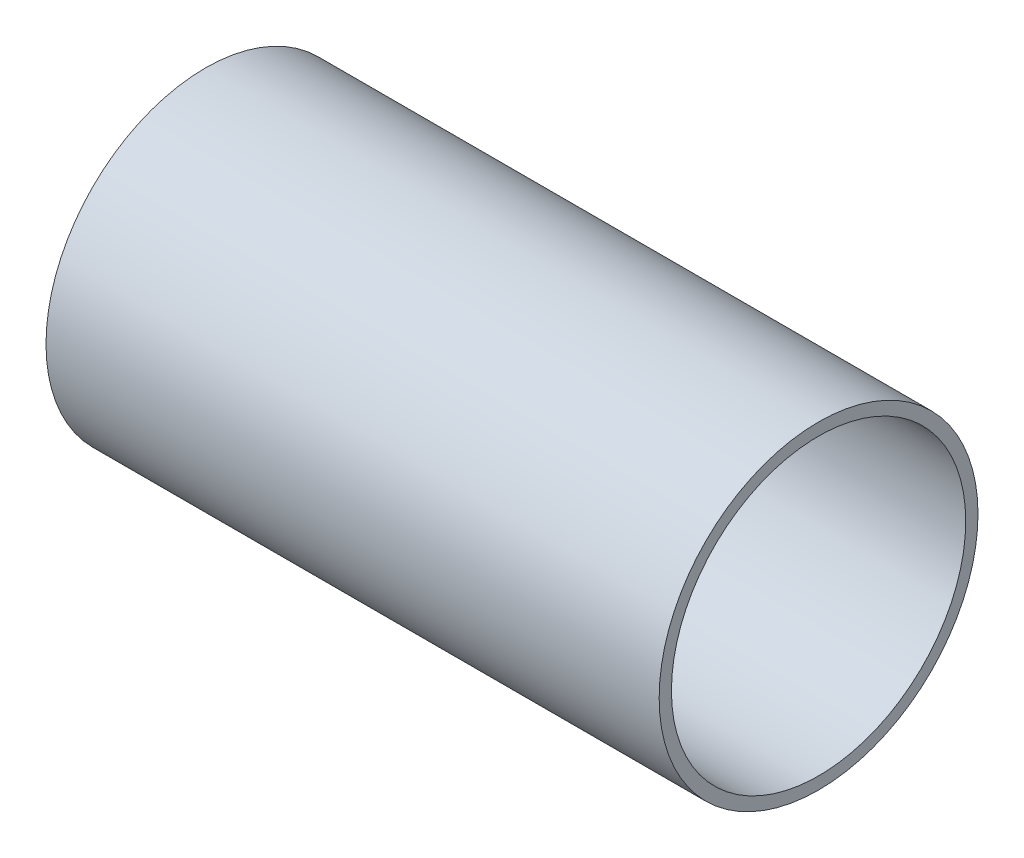
SolidWorks part; units mm, degrees
ref_plane "Front Plane" through (0, 0, 0) normal (0, 0, 1) x (1, 0, 0)
ref_plane "Top Plane" through (0, 0, 0) normal (0, 1, 0) x (1, 0, 0)
ref_plane "Right Plane" through (0, 0, 0) normal (1, 0, 0) x (0, 0, -1)
sketch "Sketch1" plane through (0, 0, 0) normal (0, 1, 0) x (1, 0, 0)
  line L0 (355.6, 50.8) -> (355.6, 1.27)
  line L1 (355.6, 1.27) -> (50.8, 1.27)
  line L2 (50.8, 13.6816) -> (50.8, 1.27)
  spline S0 degree 4 poles (21.2341, 5.9936) (21.856, 6.1634) (23.0998, 6.5019) (25.5843, 7.1746) (28.69, 8.0062) (31.7724, 8.8231) (34.8672, 9.6339) (37.2923, 10.2647) (39.7915, 10.9085) (42.145, 11.5111) (44.7925, 12.1812) (46.8566, 12.7019) (49.9381, 13.4687) (51.3469, 13.8173) (53.9013, 14.445) (55.9043, 14.9331) (57.9182, 15.4203) (59.9692, 15.9131) (62.0056, 16.3987) (64.0459, 16.8817) (66.6196, 17.4865) (69.7274, 18.2096) (73.3707, 19.0464) (77.5504, 19.9917) (82.7791, 21.1557) (97.434, 24.3488) (119.4856, 28.817) (168.0008, 37.516) (219.035, 44.0813) (262.8224, 47.8202) (299.2065, 49.5707) (308.8412, 49.9474) (315.2656, 50.1624) (319.549, 50.2912) (323.8328, 50.4056) (328.117, 50.5056) (332.4014, 50.5911) (336.1391, 50.6531) (339.3296, 50.6971) (341.9732, 50.7276) (344.0698, 50.7484) (346.1633, 50.7657) (348.2725, 50.7795) (350.3447, 50.7899) (352.4057, 50.7968) (355.0352, 50.8005) (356.4848, 50.8002) (359.6537, 50.7954) (361.7791, 50.7854) (364.5032, 50.7703) (366.9275, 50.7502) (369.503, 50.7251) (372.0018, 50.695) (374.5511, 50.6597) (377.0919, 50.6192) (379.6547, 50.5733) (382.2234, 50.522) (384.1523, 50.4796) (385.4374, 50.4496) (386.0799, 50.4342) knots 0 0 0 0 0 0.006986 0.013973 0.027946 0.034806 0.041666 0.048526 0.055386 0.062246 0.069106 0.075966 0.082827 0.088511 0.094195 0.099879 0.105563 0.111247 0.116931 0.122615 0.128299 0.139917 0.151536 0.163154 0.174773 0.19801 0.314194 0.407142 0.709223 0.755697 0.790552 0.802171 0.813789 0.825408 0.837026 0.848645 0.860263 0.871882 0.877566 0.88325 0.888934 0.894618 0.900302 0.905986 0.91167 0.917354 0.924199 0.931044 0.937889 0.944735 0.95158 0.958425 0.96527 0.972115 0.979087 0.986058 0.993029 1 1 1 1 1 construction
  spline S1 degree 4 poles (50.8, 13.6816) (51.2246, 13.7865) (52.0797, 13.9974) (53.9013, 14.445) (55.9043, 14.9331) (57.9182, 15.4203) (59.9692, 15.9131) (62.0056, 16.3987) (64.0459, 16.8817) (66.6196, 17.4865) (69.7274, 18.2096) (73.3707, 19.0464) (77.5504, 19.9917) (82.7791, 21.1557) (97.434, 24.3488) (119.4856, 28.817) (168.0008, 37.516) (219.035, 44.0813) (262.8224, 47.8202) (299.2065, 49.5707) (308.8412, 49.9474) (315.2656, 50.1624) (319.549, 50.2912) (323.8328, 50.4056) (328.117, 50.5056) (332.4014, 50.5911) (336.1391, 50.6531) (339.3296, 50.6971) (341.9732, 50.7276) (344.0698, 50.7484) (346.1633, 50.7657) (348.2725, 50.7795) (350.3447, 50.7899) (352.4057, 50.7968) (354.282, 50.7994) (355.1626, 50.8) (355.6, 50.8) knots 0.082827 0.082827 0.082827 0.082827 0.082827 0.088511 0.094195 0.099879 0.105563 0.111247 0.116931 0.122615 0.128299 0.139917 0.151536 0.163154 0.174773 0.19801 0.314194 0.407142 0.709223 0.755697 0.790552 0.802171 0.813789 0.825408 0.837026 0.848645 0.860263 0.871882 0.877566 0.88325 0.888934 0.894618 0.900302 0.905986 0.91167 0.917354 0.917354 0.917354 0.917354 0.917354
  dimension "D1" = 49.53
  dimension "D2" = 12.4116
revolve "Revolve2" add sketch "Sketch1" angle 360 about L1
ref_plane "Plane1" through (358.14, 0, 0) normal (1, 0, 0) x (0, 0, -1)
sketch "Sketch2" plane through (355.6, 0, 0) normal (1, 0, 0) x (0, 0, -1)
  line L1 (-48.26, 0) -> (50.8, 0) construction
  circle A0 centre (1.27, 0) radius 49.53 construction
  circle A1 centre (1.27, 0) radius 49.53
extrude "Boss-Extrude1" add sketch "Sketch2" along normal blind 203.2
sketch "Sketch3" plane through (50.8, 0, 0) normal (-1, 0, 0) x (0, 0, 1)
  line L0 (-13.6816, 0) -> (11.1416, 0) construction
  circle A0 centre (-1.27, 0) radius 12.4116 construction
  circle A1 centre (-1.27, 0) radius 12.4116
extrude "Boss-Extrude2" add sketch "Sketch3" along normal blind 50.8
ref_plane "Plane2" through (368.3, 0, 0) normal (1, 0, 0) x (0, 0, -1)
sketch "Sketch4" plane through (368.3, 0, 0) normal (1, 0, 0) x (0, 0, -1)
  line L0 (-48.26, 0) -> (50.8, 0) construction
  circle A0 centre (1.27, 0) radius 49.53 construction
  circle A1 centre (1.27, 0) radius 49.53
extrude "Cut-Extrude1" cut sketch "Sketch4" against normal blind 381
shell "Shell1" thickness 3.81
